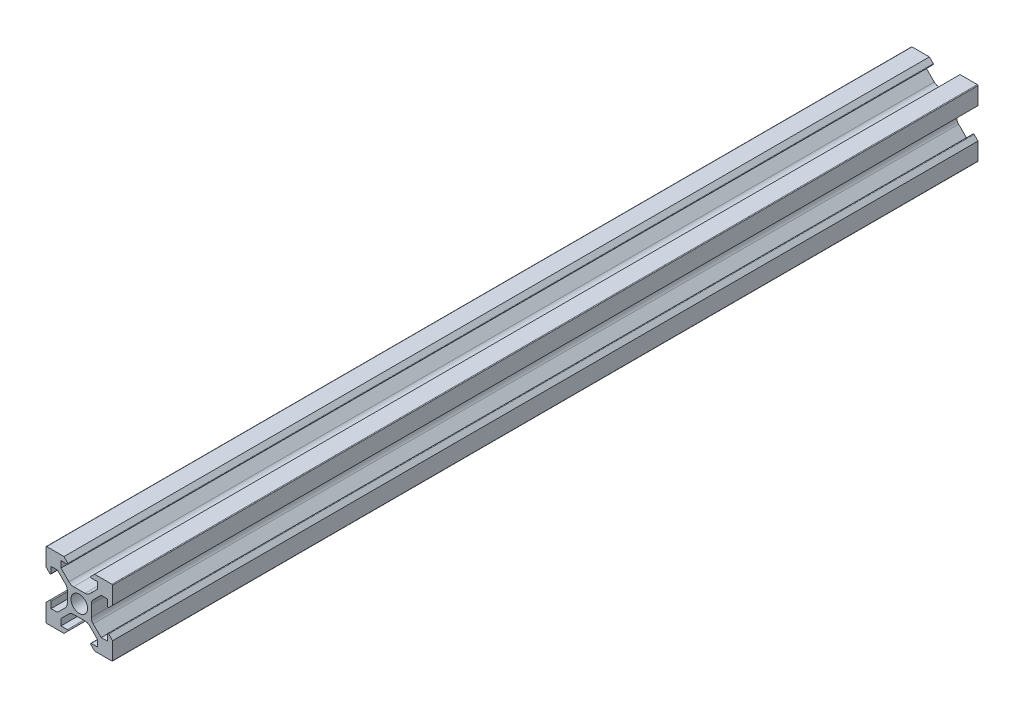
SolidWorks part; units mm, degrees
material "Liga 1350"
ref_plane "Plano frontal" through (0, 0, 0) normal (0, 0, 1) x (1, 0, 0)
ref_plane "Plano superior" through (0, 0, 0) normal (0, 1, 0) x (1, 0, 0)
ref_plane "Plano direito" through (0, 0, 0) normal (1, 0, 0) x (0, 0, -1)
sketch "Esboço1" plane through (0, 0, 0) normal (0, 0, 1) x (1, 0, 0)
  line L0 (0, 13.8681) -> (0, -15.879) construction
  line L1 (-4.6, -10) -> (-9.8, -10)
  line L2 (-3.4414, -8.8414) -> (-4.6, -10)
  line L3 (-4.1858, -3.1251) -> (-6.5607, -5.5)
  line L4 (-10, 9.8) -> (-10, 4.6)
  line L5 (-5.5, -8.5) -> (-3.5828, -8.5)
  line L6 (-5.5, -8.5) -> (-5.5, -6.5607)
  line L7 (-8.5, -5.5) -> (-8.5, -3.5828)
  line L8 (-21.5514, 0) -> (2.5, 0) construction
  line L9 (-3.1251, 4.1858) -> (-5.5, 6.5607)
  line L10 (-8.8414, -3.4414) -> (-10, -4.6)
  line L11 (-8.5, 5.5) -> (-6.5607, 5.5)
  line L12 (-8.8414, 3.4414) -> (-10, 4.6)
  line L13 (-8.5, -5.5) -> (-6.5607, -5.5)
  line L14 (-8.5, 5.5) -> (-8.5, 3.5828)
  line L15 (-3.1251, -4.1858) -> (-5.5, -6.5607)
  line L16 (-21.5514, 0) -> (20.6623, 0) construction
  line L17 (-8.5, 10) -> (-8.5, -10) construction
  line L18 (-10, -9.8) -> (-10, -4.6)
  line L19 (-21.5514, 5.5) -> (20.6623, 5.5) construction
  line L21 (-10, 10) -> (-10, -10) construction
  line L22 (3.6, 1.7109) -> (3.6, 0) construction
  line L23 (21.5514, 0) -> (-2.5, 0) construction
  line L24 (4.6, 10) -> (9.8, 10)
  line L25 (-5.5, 8.5) -> (-5.5, 6.5607)
  line L26 (3.4414, 8.8414) -> (4.6, 10)
  line L27 (-5.5, 8.5) -> (-3.5828, 8.5)
  line L28 (4.1858, 3.1251) -> (6.5607, 5.5)
  line L29 (5.5, 8.5) -> (3.5828, 8.5)
  line L30 (5.5, 8.5) -> (5.5, 6.5607)
  line L31 (-3.6, 1.7109) -> (-3.6, -1.7109)
  line L33 (10, -9.8) -> (10, -4.6)
  line L34 (-4.1858, 3.1251) -> (-6.5607, 5.5)
  line L35 (-3.4414, 8.8414) -> (-4.6, 10)
  line L36 (-4.6, 10) -> (-9.8, 10)
  line L37 (3.1251, -4.1858) -> (5.5, -6.5607)
  line L38 (8.5, 5.5) -> (8.5, 3.5828)
  line L39 (8.5, -5.5) -> (6.5607, -5.5)
  line L40 (8.8414, 3.4414) -> (10, 4.6)
  line L41 (8.5, 5.5) -> (6.5607, 5.5)
  line L42 (8.8414, -3.4414) -> (10, -4.6)
  line L43 (3.1251, 4.1858) -> (5.5, 6.5607)
  line L44 (8.5, -5.5) -> (8.5, -3.5828)
  line L45 (5.5, -8.5) -> (5.5, -6.5607)
  line L46 (5.5, -8.5) -> (3.5828, -8.5)
  line L47 (10, 9.8) -> (10, 4.6)
  line L48 (4.1858, -3.1251) -> (6.5607, -5.5)
  line L49 (3.4414, -8.8414) -> (4.6, -10)
  line L50 (4.6, -10) -> (9.8, -10)
  line L51 (-1.7109, 3.6) -> (1.7109, 3.6)
  line L52 (3.6, 1.7109) -> (3.6, -1.7109)
  line L53 (1.7109, -3.6) -> (-1.7109, -3.6)
  circle A0 centre (0, 0) radius 2.5
  arc A1 (-3.6, 1.7109) -> (-4.1858, 3.1251) centre (-5.6, 1.7109) ccw
  arc A2 (-8.5, 3.5828) -> (-8.8414, 3.4414) centre (-8.7, 3.5828) cw
  arc A3 (-9.8, 10) -> (-10, 9.8) centre (-9.8, 9.8) ccw
  arc A4 (-1.7109, 3.6) -> (-3.1251, 4.1858) centre (-1.7109, 5.6) cw
  arc A5 (-3.5828, 8.5) -> (-3.4414, 8.8414) centre (-3.5828, 8.7) ccw
  arc A6 (-3.5828, -8.5) -> (-3.4414, -8.8414) centre (-3.5828, -8.7) cw
  arc A7 (-1.7109, -3.6) -> (-3.1251, -4.1858) centre (-1.7109, -5.6) ccw
  arc A8 (-9.8, -10) -> (-10, -9.8) centre (-9.8, -9.8) cw
  arc A9 (-8.5, -3.5828) -> (-8.8414, -3.4414) centre (-8.7, -3.5828) ccw
  arc A10 (-3.6, -1.7109) -> (-4.1858, -3.1251) centre (-5.6, -1.7109) cw
  arc A11 (3.6, -1.7109) -> (4.1858, -3.1251) centre (5.6, -1.7109) ccw
  arc A12 (8.5, -3.5828) -> (8.8414, -3.4414) centre (8.7, -3.5828) cw
  arc A13 (9.8, -10) -> (10, -9.8) centre (9.8, -9.8) ccw
  arc A14 (1.7109, -3.6) -> (3.1251, -4.1858) centre (1.7109, -5.6) cw
  arc A15 (3.5828, -8.5) -> (3.4414, -8.8414) centre (3.5828, -8.7) ccw
  arc A16 (3.5828, 8.5) -> (3.4414, 8.8414) centre (3.5828, 8.7) cw
  arc A17 (1.7109, 3.6) -> (3.1251, 4.1858) centre (1.7109, 5.6) ccw
  arc A18 (9.8, 10) -> (10, 9.8) centre (9.8, 9.8) cw
  arc A19 (8.5, 3.5828) -> (8.8414, 3.4414) centre (8.7, 3.5828) ccw
  arc A20 (3.6, 1.7109) -> (4.1858, 3.1251) centre (5.6, 1.7109) cw
  point P0 (0, 0)
  point P45 (-3.6, 2.5393)
extrude "Ressalto-extrusão1" add sketch "Esboço1" along normal blind 260
equation "\"0.435m-15c\"=0.435"
